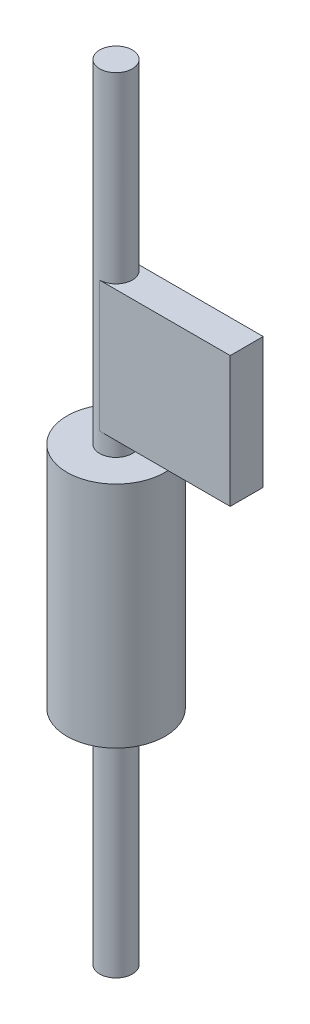
SolidWorks part; units mm, degrees
ref_plane "Front Plane" through (0, 0, 0) normal (0, 0, 1) x (1, 0, 0)
ref_plane "Top Plane" through (0, 0, 0) normal (0, 1, 0) x (1, 0, 0)
ref_plane "Right Plane" through (0, 0, 0) normal (1, 0, 0) x (0, 0, -1)
sketch "Sketch1" plane through (0, 0, 0) normal (0, 1, 0) x (1, 0, 0)
  circle A0 centre (0, 0) radius 3.175
  dimension "D1" = 6.35
extrude "Boss-Extrude1" add sketch "Sketch1" along normal blind 152.4 contours A0
sketch "Sketch2" plane through (0, 0, 0) normal (1, 0, 0) x (0, 0, -1)
  line L0 (0, 3.4925) -> (0, -3.4925) construction
  line L1 (-3.2067, 116.84) -> (3.2067, 116.84)
  line L2 (-3.2067, 116.84) -> (-3.2067, 91.44)
  line L3 (-3.2067, 91.44) -> (3.2068, 91.44)
  line L4 (3.2067, 116.84) -> (3.2068, 91.44)
  line L5 (3.175, 152.4) -> (-3.175, 152.4) construction
  dimension "D1" = 6.4135
  dimension "D2" = 3.2067
  dimension "D3" = 25.4
  dimension "D4" = 35.56
extrude "Boss-Extrude2" add sketch "Sketch2" along normal blind 25.4
ref_plane "Plane1" through (0, 43.18, 0) normal (0, 1, 0) x (1, 0, 0)
sketch "Sketch4" plane through (0, 43.18, 0) normal (0, 1, 0) x (1, 0, 0)
  circle A0 centre (0, 0) radius 9.525
  dimension "D1" = 19.05
extrude "Boss-Extrude3" add sketch "Sketch4" along normal blind 44.45
equation "\"D2@Sketch2\"=.5*\"D1@Sketch2\""
